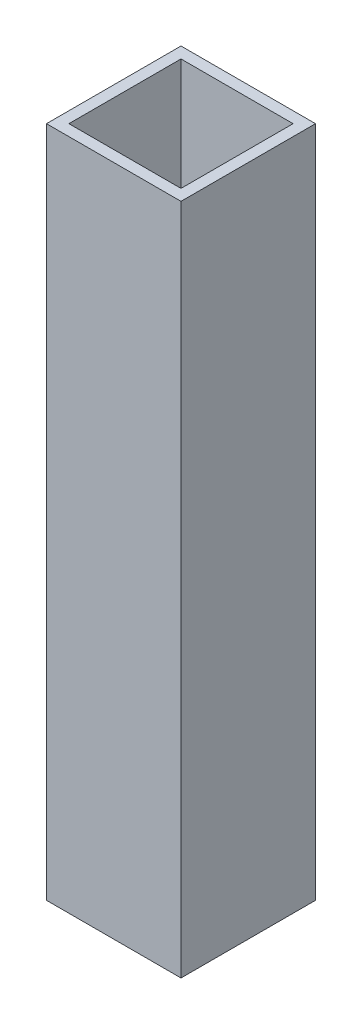
SolidWorks part; units mm, degrees
material "6063-T6"
ref_plane "Front Plane" through (0, 0, 0) normal (0, 0, 1) x (1, 0, 0)
ref_plane "Top Plane" through (0, 0, 0) normal (0, 1, 0) x (1, 0, 0)
ref_plane "Right Plane" through (0, 0, 0) normal (1, 0, 0) x (0, 0, -1)
sketch "Sketch1" plane through (0, 0, 0) normal (0, 1, 0) x (1, 0, 0)
  line L0 (3.175, 34.925) -> (34.925, 34.925)
  line L1 (0, 0) -> (38.1, 0)
  line L2 (0, 0) -> (0, 38.1)
  line L3 (0, 38.1) -> (38.1, 38.1)
  line L4 (38.1, 0) -> (38.1, 38.1)
  line L5 (34.925, 3.175) -> (34.925, 34.925)
  line L6 (3.175, 3.175) -> (34.925, 3.175)
  line L7 (3.175, 3.175) -> (3.175, 34.925)
  dimension "D1" = 38.1
  dimension "D2" = 3.175
extrude "Boss-Extrude1" add sketch "Sketch1" along normal blind 190.5
